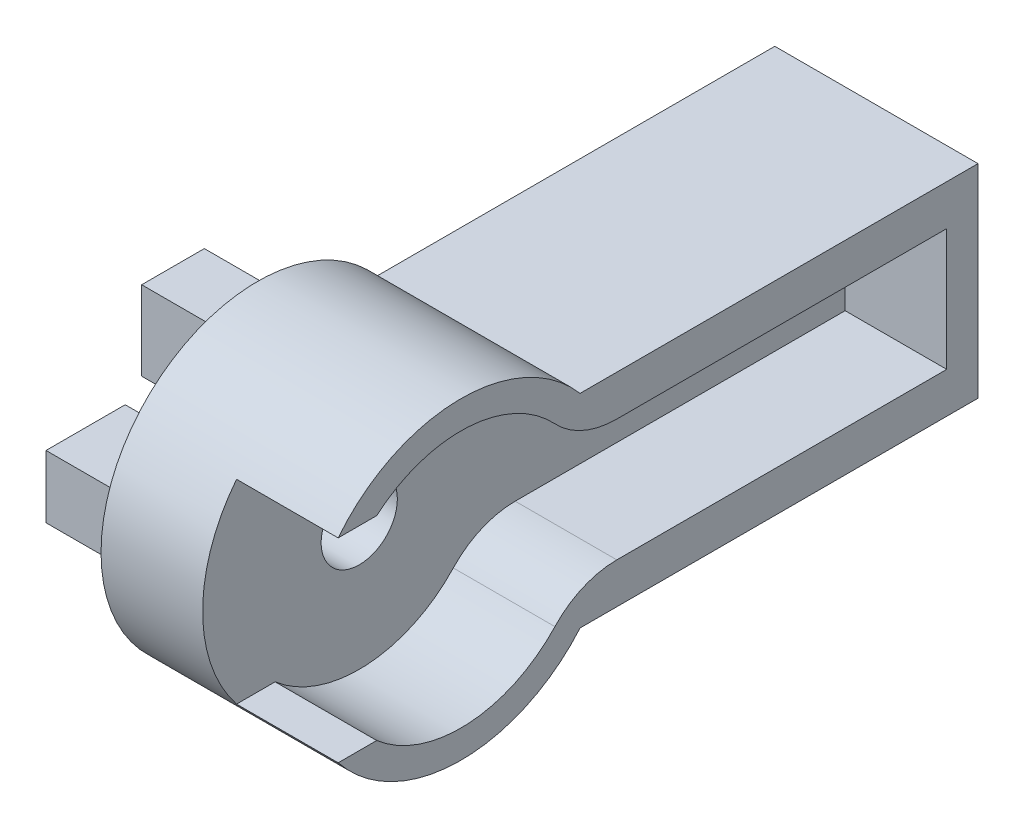
SolidWorks part; units mm, degrees
ref_plane "Front Plane" through (0, 0, 0) normal (0, 0, 1) x (1, 0, 0)
ref_plane "Top Plane" through (0, 0, 0) normal (0, 1, 0) x (1, 0, 0)
ref_plane "Right Plane" through (0, 0, 0) normal (1, 0, 0) x (0, 0, -1)
sketch "Sketch1" plane through (0, 0, 0) normal (1, 0, 0) x (0, 0, -1)
  line L1 (7.0401, 6) -> (30.5401, 6)
  line L2 (7.0401, 6) -> (7.0401, -6)
  line L3 (7.0401, -6) -> (30.5401, -6)
  line L4 (30.5401, 6) -> (30.5401, -6)
  circle A0 centre (0, 0) radius 9.25
  point P7 (8.124, -3.873)
  dimension "D1" = 18.5
  dimension "D2" = 23.5
  dimension "D3" = 12
extrude "Boss-Extrude1" add sketch "Sketch1" along normal blind 12 contours A0 L3 L4 L1 | L2 A0
sketch "Sketch2" plane through (12, 0, 0) normal (1, 0, 0) x (0, 0, -1)
  line L1 (6.6933, 3.6) -> (28.6933, 3.6)
  line L2 (6.6933, 3.6) -> (6.6933, -3.6)
  line L3 (6.6933, -3.6) -> (28.6933, -3.6)
  line L4 (28.6933, 3.6) -> (28.6933, -3.6)
  line L5 (-4.9697, 5.75) -> (-11.0599, 5.75)
  line L6 (-4.9697, 5.75) -> (-4.9697, -5.75)
  line L7 (-4.9697, -5.75) -> (-11.0599, -5.75)
  line L8 (-11.0599, 5.75) -> (-11.0599, -5.75)
  circle A0 centre (0, 0) radius 7.6
  point P7 (-6.1103, -4.5194)
  dimension "D1" = 15.2
  dimension "D2" = 22
  dimension "D3" = 7.2
  dimension "D4" = 11.5
extrude "Cut-Extrude1" cut sketch "Sketch2" against normal blind 6 contours A0 L3 L4 L1 | L2 A0 | L6 L5 L8 L7
fillet "Fillet1" radius 5 2 edges at (9, 3.6, -6.6933) (9, -3.6, -6.6933)
sketch "Sketch3" plane through (6, 0, 0) normal (1, 0, 0) x (0, 0, -1)
  line L0 (0, 0) -> (35.2633, 0) construction
  circle A0 centre (0, 0) radius 2.25
  circle A1 centre (20.5, 0) radius 1.65
  circle A2 centre (24.5, 0) radius 1.65
  dimension "D1" = 4.5
  dimension "D2" = 3.3
  dimension "D3" = 3.3
  dimension "D4" = 20.5
  dimension "D5" = 24.5
extrude "Cut-Extrude2" cut sketch "Sketch3" against normal up to surface (6 mm away) up to face at (0, 0, -14.7175)
sketch "Sketch5" plane through (0, 0, 0) normal (-1, 0, 0) x (0, 0, 1)
  line L9 (-7.5, 1.85) -> (7.5, 1.85)
  line L10 (-7.5, 1.85) -> (-7.5, -1.85)
  line L11 (-7.5, -1.85) -> (7.5, -1.85)
  line L12 (7.5, 1.85) -> (7.5, -1.85)
  line L13 (-7.5, 1.85) -> (7.5, -1.85) construction
  line L14 (-7.5, -1.85) -> (7.5, 1.85) construction
  line L15 (-1.85, 7.5) -> (1.85, 7.5)
  line L16 (-1.85, 7.5) -> (-1.85, -7.5)
  line L17 (-1.85, -7.5) -> (1.85, -7.5)
  line L18 (1.85, 7.5) -> (1.85, -7.5)
  line L19 (-1.85, 7.5) -> (1.85, -7.5) construction
  line L20 (-1.85, -7.5) -> (1.85, 7.5) construction
  point P0 (0, 0)
  point P6 (0, 0)
  circle M12 centre (0, 0) radius 2.25
  dimension "D3" = 15
  dimension "D1" = 3.7
  dimension "D2" = 3.7
  dimension "D4" = 15
extrude "Boss-Extrude2" add sketch "Sketch5" along normal blind 5 contours L16 L9 L10 L11 M12 | L18 L15 L16 L9 M12 | L9 L18 L11 L12 M12 | L18 L11 L16 L17 M12 | L9 L16 M12 | L18 L9 M12 | L18 L11 M12 | L16 L11 M12
sketch "Sketch6" plane through (-5, 0, 0) normal (-1, 0, 0) x (0, 0, 1)
  circle A0 centre (0, 0) radius 3.375
  dimension "D1" = 6.75
extrude "Cut-Extrude3" cut sketch "Sketch6" against normal up to surface (5 mm away) up to face at (0, 0, 0)
